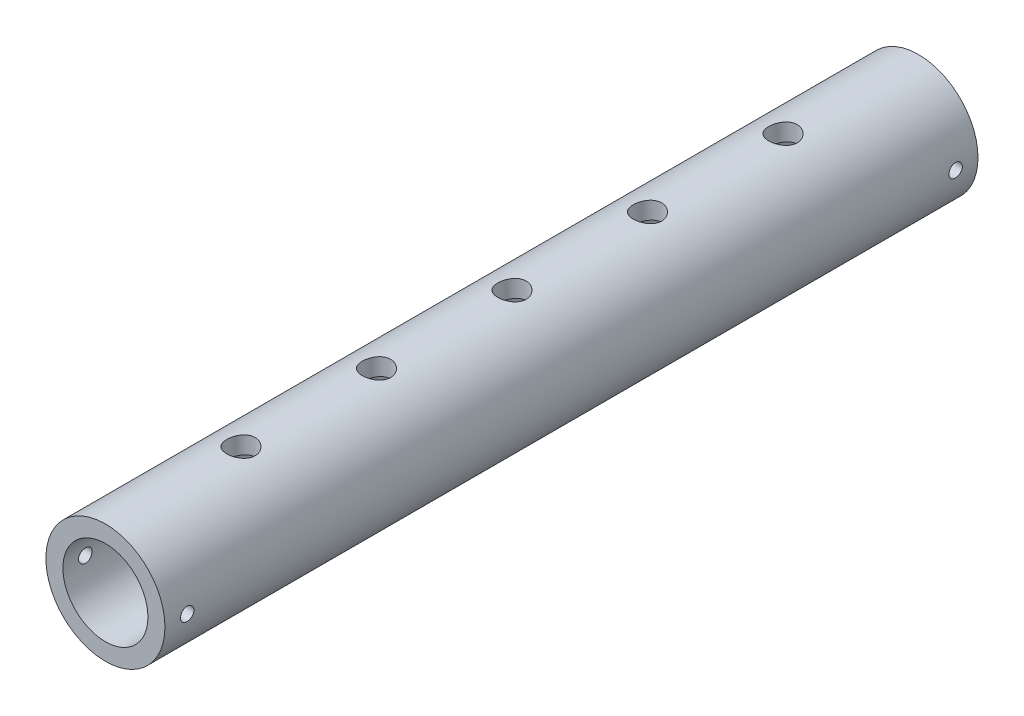
SolidWorks part; units mm, degrees
ref_plane "Front Plane" through (0, 0, 0) normal (0, 0, 1) x (1, 0, 0)
ref_plane "Top Plane" through (0, 0, 0) normal (0, 1, 0) x (1, 0, 0)
ref_plane "Right Plane" through (0, 0, 0) normal (1, 0, 0) x (0, 0, -1)
sketch "Sketch2" plane through (0, 0, 0) normal (0, 0, 1) x (1, 0, 0)
  circle A0 centre (0, 0) radius 13.335
  circle A1 centre (0, 0) radius 9.525
  dimension "D1" = 26.67
  dimension "D2" = 19.05
extrude "Boss-Extrude1" add sketch "Sketch2" along normal blind 182.118
sketch "Sketch3" plane through (0, 0, 0) normal (0, 1, 0) x (1, 0, 0)
  line L0 (-9.525, -182.118) -> (9.525, -182.118) construction
  line L1 (-9.525, -182.118) -> (9.525, -182.118)
  line L2 (0, -182.118) -> (0, 0)
  circle A0 centre (0, -151.765) radius 3.175
  circle A1 centre (0, -121.412) radius 3.175
  circle A2 centre (0, -91.059) radius 3.175
  circle A3 centre (0, -60.706) radius 3.175
  circle A4 centre (0, -30.353) radius 3.175
  point P5 (0, -151.765)
  point P6 (0, -121.412)
  point P7 (0, -91.059)
  point P8 (0, -60.706)
  point P9 (0, -30.353)
  dimension "D1" = 6.35
  dimension "D2" = 6.35
  dimension "D3" = 6.35
  dimension "D4" = 6.35
  dimension "D5" = 6.35
extrude "Cut-Extrude1" cut sketch "Sketch3" along normal through all and the other way through all contours L2 A0 | L2 A0 | A1 | A2 | A3 | A4
sketch "Sketch4" plane through (0, 0, 0) normal (1, 0, 0) x (0, 0, -1)
  line L0 (-182.118, 13.335) -> (-182.118, -13.335) construction
  circle A0 centre (-177.118, 0) radius 1.5
  circle A1 centre (-5, 0) radius 1.5
  dimension "D1" = 3
  dimension "D2" = 3
  dimension "D3" = 5
  dimension "D4" = 5
extrude "Cut-Extrude2" cut sketch "Sketch4" against normal through all and the other way through all
